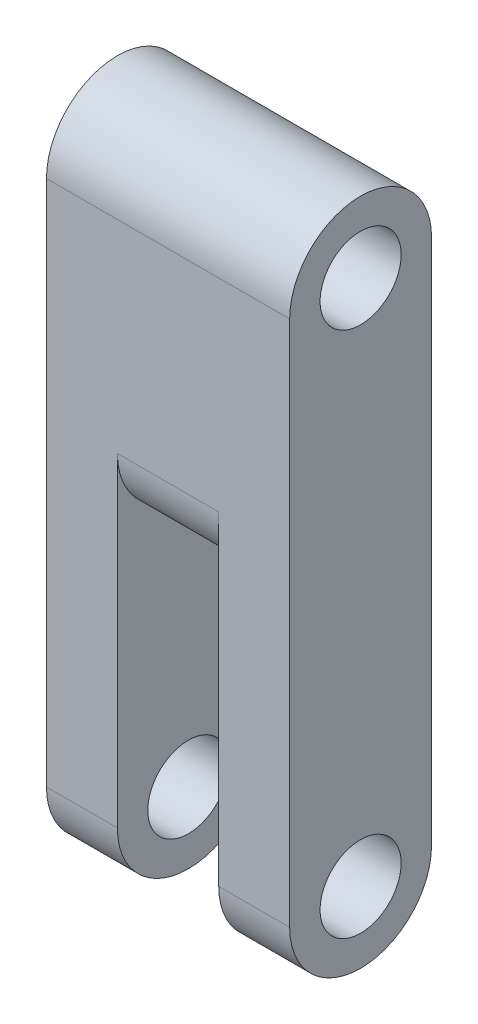
SolidWorks part; units mm, degrees
material "ABS"
ref_plane "Спереди" through (0, 0, 0) normal (0, 0, 1) x (1, 0, 0)
ref_plane "Сверху" through (0, 0, 0) normal (0, 1, 0) x (1, 0, 0)
ref_plane "Справа" through (0, 0, 0) normal (1, 0, 0) x (0, 0, -1)
sketch "Эскиз1" plane through (0, 0, 0) normal (1, 0, 0) x (0, 0, -1)
  line L0 (3.5, 28.15) -> (3.5, -49971.85) construction
  line L2 (0, 0) -> (0, 26)
  line L4 (7, 0) -> (7, 26)
  line L5 (0, 0) -> (7, 26) construction
  line L6 (0, 26) -> (7, 0) construction
  line L7 (3.5, 13) -> (50003.5, 13) construction
  circle A0 centre (3.5, 26) radius 2
  arc A1 (0, 26) -> (7, 26) centre (3.5, 26) cw
  circle A2 centre (3.5, 0) radius 2
  arc A3 (0, 0) -> (7, 0) centre (3.5, 0) ccw
  point P4 (3.5, 13)
  dimension "D3" = 4
  dimension "D4" = 3.5
  dimension "D1" = 13
  dimension "D2" = 7
  dimension "D5" = 26
  dimension "D6" = 13
extrude "Бобышка-Вытянуть1" add sketch "Эскиз1" along normal blind 12 contours L2 A1 L4 A3
sketch "Эскиз2" plane through (12, 0, 0) normal (1, 0, 0) x (0, 0, -1)
  line L0 (0, -1000) -> (0, 49000) construction
  line L1 (-1000, 0) -> (49000, 0) construction
  line L2 (3.5, -1005.3228) -> (3.5, 48994.6772) construction
  line L3 (-1009.6355, 26) -> (48990.3645, 26) construction
  circle A4 centre (3.5, 0) radius 2
  circle A5 centre (3.5, 26) radius 2
  point P3 (3.5, 26)
  point P5 (3.5, 0)
  dimension "D3" = 4
  dimension "D4" = 4
  dimension "D2" = 3.5
  dimension "D1" = 26
extrude "Вырез-Вытянуть2" cut sketch "Эскиз2" against normal blind 15
ref_plane "Плоскость1" through (3.5, 0, 0) normal (1, 0, 0) x (0, 0, -1)
sketch "Эскиз3" plane through (3.5, 0, 0) normal (1, 0, 0) x (0, 0, -1)
  line L0 (-996.5, 26) -> (49003.5, 26) construction
  line L1 (0, -1000) -> (0, 49000) construction
  line L2 (0, 16) -> (-8.336, 16)
  line L3 (-1005.198, 16) -> (48994.802, 16) construction
  line L4 (7, -978.9268) -> (7, 49021.0732) construction
  line L14 (3.5, -986.1873) -> (3.5, 49013.8127) construction
  line L15 (-1011.7304, 12.5) -> (48988.2696, 12.5) construction
  line L16 (-8.336, 16) -> (-8.336, -12.2749)
  line L17 (-8.336, -12.2749) -> (16.664, -12.2749)
  line L18 (16.664, -12.2749) -> (16.664, 16)
  line L19 (16.664, 16) -> (7, 16)
  arc A2 (0, 16) -> (7, 16) centre (3.5, 16) ccw
  point P4 (0, 16)
  point P8 (7, 16)
  point P11 (3.5, 16)
  point P12 (3.5, 12.5)
  dimension "D4" = 3.5
  dimension "D5" = 25
  dimension "D3" = 3.5
  dimension "D1" = 10
  dimension "D2" = 7
  dimension "D6" = 28.2749
  dimension "D7" = 13.164
extrude "Вырез-Вытянуть3" cut sketch "Эскиз3" along normal blind 5
